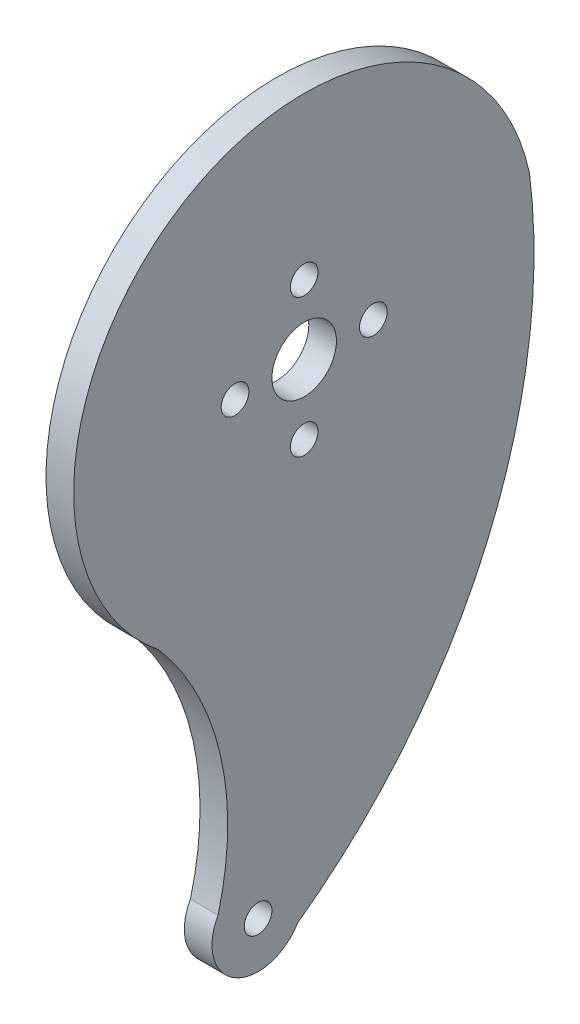
SolidWorks part; units mm, degrees
ref_plane "Alzado" through (0, 0, 0) normal (0, 0, 1) x (1, 0, 0)
ref_plane "Planta" through (0, 0, 0) normal (0, 1, 0) x (1, 0, 0)
ref_plane "Vista lateral" through (0, 0, 0) normal (1, 0, 0) x (0, 0, -1)
sketch "Croquis1" plane through (0, 0, 0) normal (1, 0, 0) x (0, 0, -1)
  line L0 (0, 0) -> (0, -50) construction
  line L1 (0, -50) -> (-5, -50) construction
  line L3 (0, 0) -> (0, 21.7358) construction
  arc A0 (24.4295, 5.3105) -> (-15.7493, -19.4155) centre (0, 0) ccw
  arc A1 (-9.3383, -47.5143) -> (-0.7107, -52.5695) centre (-5, -50) ccw
  arc A2 (24.4295, 5.3105) -> (-0.7107, -52.5695) centre (-36.7974, -2.4954) cw
  arc A3 (-9.3383, -47.5143) -> (-15.7493, -19.4155) centre (-39.2314, -39.5538) ccw
  circle A4 centre (0, 0) radius 3.5
  circle A5 centre (-5, -50) radius 1.5
  circle A7 centre (-7.5, 0) radius 1.5
  circle A8 centre (0, 7.5) radius 1.5
  circle A9 centre (7.5, 0) radius 1.5
  circle A10 centre (0, -7.5) radius 1.5
  dimension "D1" = 50
  dimension "D2" = 25
  dimension "D3" = 7
  dimension "D4" = 3
extrude "Saliente-Extruir1" add sketch "Croquis1" along normal blind 3
